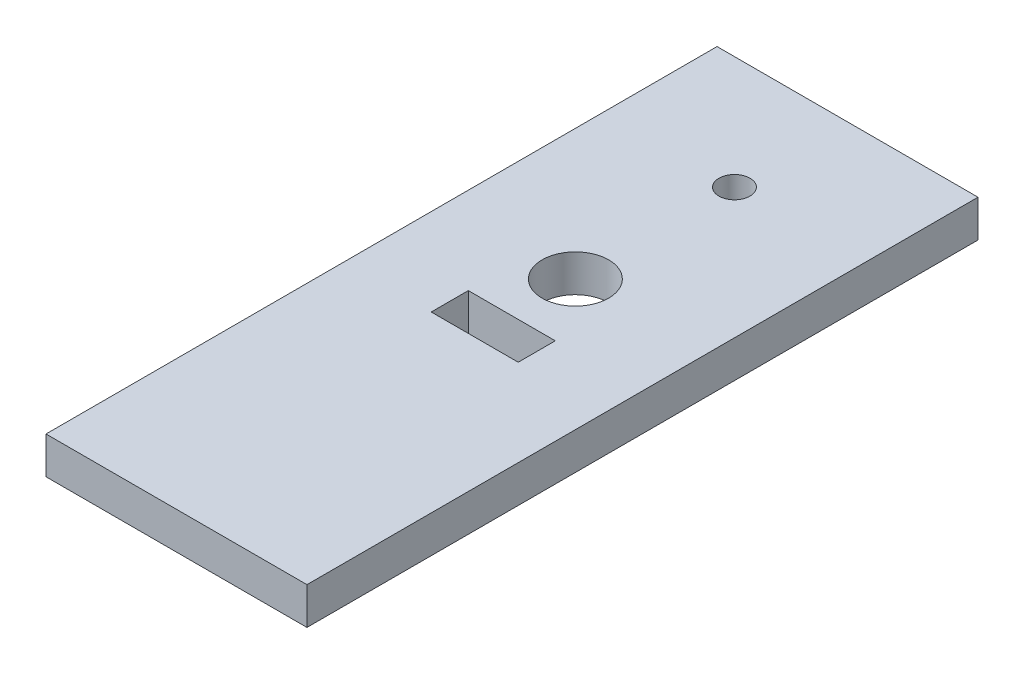
SolidWorks part; units mm, degrees
ref_plane "Front Plane" through (0, 0, 0) normal (0, 0, 1) x (1, 0, 0)
ref_plane "Top Plane" through (0, 0, 0) normal (0, 1, 0) x (1, 0, 0)
ref_plane "Right Plane" through (0, 0, 0) normal (1, 0, 0) x (0, 0, -1)
sketch "Sketch1" plane through (0, 0, 0) normal (0, 1, 0) x (1, 0, 0)
  line L0 (0, 0) -> (42, 0) construction
  line L1 (0, 0) -> (14, 0)
  line L2 (0, 0) -> (0, 60)
  line L3 (0, 60) -> (42, 60)
  line L4 (42, 0) -> (42, 60)
  line L5 (14, 0) -> (14, 5.969)
  line L6 (14, 5.969) -> (28, 5.969)
  line L7 (28, 5.969) -> (28, 0)
  line L8 (28, 0) -> (42, 0)
  line L9 (21, 60) -> (21, 0) construction
  circle A0 centre (21, 16.2) radius 5.35
  circle A1 centre (21, 41.8) radius 2.5
  dimension "D4" = 16.2
  dimension "D5" = 10.7
  dimension "D6" = 25.6
  dimension "D7" = 5
  dimension "D1" = 42
  dimension "D2" = 60
  dimension "D3" = 5.969
extrude "Boss-Extrude1" add sketch "Sketch1" along normal blind 5.969
sketch "Sketch2" plane through (0, 5.969, 0) normal (0, 1, 0) x (1, 0, 0)
  line L1 (0, 0) -> (42, 0)
  line L2 (0, 0) -> (0, -48)
  line L3 (0, -48) -> (42, -48)
  line L4 (42, 0) -> (42, -48)
  line L5 (0, 0) -> (42, -48) construction
  line L6 (0, -48) -> (42, 0) construction
  point P4 (21, -24)
  dimension "D1" = 48
extrude "Boss-Extrude2" add sketch "Sketch2" against normal up to surface (5.969 mm away) up to face at (21, 0, -10.85)
